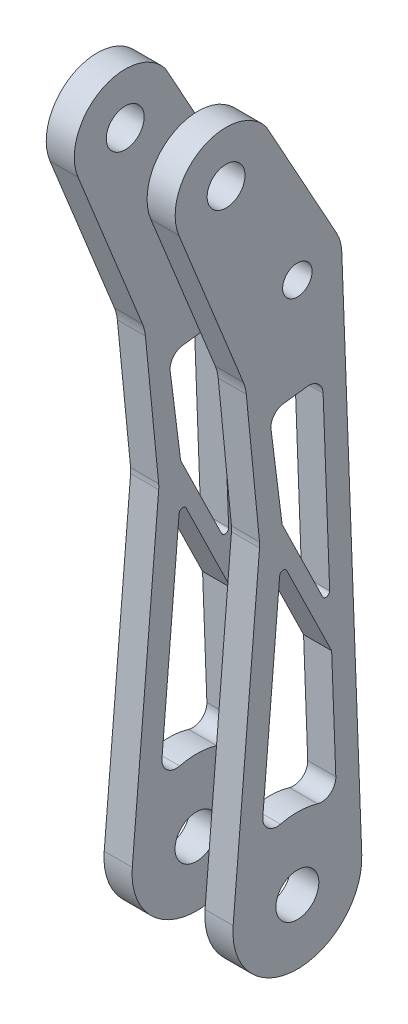
SolidWorks part; units mm, degrees
material "6061-T6 (SS)"
ref_plane "X-Y Datum" through (0, 0, 0) normal (0, 0, 1) x (1, 0, 0)
ref_plane "X-Z Datum" through (0, 0, 0) normal (0, 1, 0) x (1, 0, 0)
ref_plane "Y-Z Datum" through (0, 0, 0) normal (1, 0, 0) x (0, 0, -1)
sketch "Sketch6" plane through (0, 0, 0) normal (1, 0, 0) x (0, 0, -1)
  line L0 (0, 0) -> (0, 95.25) construction
  line L1 (0, 0) -> (0, 118.022) construction
  line L20 (-8.3819, 70.7797) -> (-14.2372, 1.1981)
  line L21 (9.8547, 118.3918) -> (11.5534, 73.1262)
  line L23 (11.5534, 73.1262) -> (14.2775, 0.5358)
  line L24 (-6.91, 150.8965) -> (8.7361, 122.5972)
  line L25 (-26.2646, 139.7057) -> (-11.9697, 104.3659)
  line L26 (-11.3233, 101.7387) -> (-8.39, 71.9341)
  arc A0 (-14.2372, 1.1981) -> (14.2775, 0.5358) centre (0, 0) ccw
  arc A2 (8.7361, 122.5972) -> (9.8547, 118.3918) centre (0, 118.022) cw
  arc A4 (-8.3819, 70.7797) -> (-8.39, 71.9341) centre (-14.7095, 71.3122) ccw
  circle A7 centre (0, 118.022) radius 3.2639
  arc A11 (-26.2646, 139.7057) -> (-6.91, 150.8965) centre (-15.7996, 143.9388) cw
  circle A12 centre (-15.7996, 143.9388) radius 4.1999
  arc A13 (-11.9697, 104.3659) -> (-11.3233, 101.7387) centre (-20.7608, 100.8099) cw
  point P8 (0, 82.55)
  point P12 (0, 82.55)
  point P14 (21.1318, 6.4606)
  point P18 (0, 63.5)
  point P20 (0, 101.6)
  point P23 (0, 0)
  point P24 (0, 0)
  point P25 (11.5534, 73.1262)
  point P26 (-26.2172, 139.5903)
  point P27 (-8.3819, 72.082)
  dimension "D2" = 30.3531
  dimension "D7" = 6.35
  dimension "D8" = 69.5816
  dimension "D5" = 32.3365
  dimension "D3" = 6.5278
  dimension "D4" = 8.3998
  dimension "D10" = 72.5904
  dimension "D11" = 173.041
  dimension "D12" = 206.788
  dimension "D1" = 14.2875
  dimension "D13" = 11.2887
  dimension "D19" = 9.4831
  dimension "D6" = 117.856
  dimension "D9" = 4.81
  dimension "D14" = 25.493
  dimension "D15" = 63.5
  dimension "D16" = 82.55
  dimension "D17" = 101.6
  dimension "D18" = 38.1215
  dimension "D20" = 29.9486
extrude "Boss-Extrude3" add sketch "Sketch6" along normal mid plane 28.575
sketch "Sketch7" plane through (14.2875, 0, 0) normal (1, 0, 0) x (0, 0, -1)
  circle A0 centre (0, 0) radius 4.7625
  dimension "D1" = 9.525
extrude "Cut-Extrude1" cut sketch "Sketch7" against normal blind 7.1437 contours A0
sketch "Sketch8" plane through (7.1437, 0, 0) normal (1, 0, 0) x (0, 0, -1)
  circle A0 centre (0, 0) radius 7.9375
  dimension "D1" = 15.875
extrude "Cut-Extrude2" cut sketch "Sketch8" against normal blind 5.5562 contours A0
mirror "Mirror1" about plane through (0, 0, 0) normal (1, 0, 0) of "Cut-Extrude2"
mirror "Mirror2" about plane through (0, 0, 0) normal (1, 0, 0) of "Cut-Extrude1"
fillet "Fillet1" [suppressed] radius 1.5875
ref_plane "Plane1" through (0, 0, 14.2372) normal (0, 0, -1) x (-1, 0, 0)
sketch "Sketch10" plane through (0, 0, 14.2372) normal (0, 0, -1) x (-1, 0, 0)
  line L0 (-8.0645, 155.9765) -> (-8.0645, -18.6485)
  line L2 (-14.2875, 150.8965) -> (14.2875, 150.8965) construction
  line L4 (8.0645, -18.6485) -> (8.0645, 155.9765)
  line L5 (-8.0645, 155.9765) -> (8.0645, 155.9765)
  line L6 (-4.8895, -21.8235) -> (4.8895, -21.8235)
  arc A1 (4.8895, -21.8235) -> (8.0645, -18.6485) centre (4.8895, -18.6485) ccw
  arc A2 (-4.8895, -21.8235) -> (-8.0645, -18.6485) centre (-4.8895, -18.6485) cw
  point P9 (0, 155.9765)
  dimension "D3" = 177.8
  dimension "D1" = 16.129
  dimension "D2" = 5.08
extrude "Cut-Extrude3" cut sketch "Sketch10" along normal mid plane 58.42
sketch "Sketch11" [suppressed] plane through (-12.7, 0, 0) normal (-1, 0, 0) x (0, 0, 1)
  line L0 (-10.7679, 9.3907) -> (-8.2566, 76.313)
  line L1 (10.3203, 9.8805) -> (4.73, 76.313)
  line L2 (7.8475, 77.1297) -> (14.2372, 1.1981) construction
  line L4 (-14.2775, 0.5358) -> (-9.5183, 127.3572) construction
  arc A0 (10.3203, 9.8805) -> (-10.7679, 9.3907) centre (0, 0) ccw
  arc A1 (-8.2566, 76.313) -> (4.73, 76.313) centre (-1.7633, 89.0398) ccw
  dimension "D1" = 28.575
  dimension "D2" = 28.575
  dimension "D3" = 3.175
  dimension "D4" = 3.175
extrude "Cut-Extrude4" [suppressed] cut sketch "Sketch11" against normal blind 4.7625 contours A1 L1 A0 L0
mirror "Mirror3" [suppressed] about plane through (0, 0, 0) normal (1, 0, 0)
sketch "Sketch12" [suppressed] plane through (0, 0, 0) normal (1, 0, 0) x (0, 0, -1)
  line L0 (0, 95.25) -> (0, 120.65) construction
  line L1 (0, 120.65) -> (24.4512, 127.5273) construction
  line L2 (0, 95.25) -> (-24.8767, 90.1209) construction
  line L3 (0, 127) -> (326.3698, 134.0383) construction
  line L4 (0, 95.25) -> (0, 69.85) construction
  dimension "D1" = 50.8
  dimension "D2" = 78.35
  dimension "D3" = 25.4
  dimension "D4" = 25.4
sketch "Sketch13" plane through (14.2875, 0, 0) normal (1, 0, 0) x (0, 0, -1)
  line L0 (-3.3694, 72.7427) -> (-6.2305, 95.423)
  line L2 (-6.2305, 95.423) -> (5.5772, 96.9125)
  line L9 (-3.3198, 70.3537) -> (-8.0907, 13.6586)
  line L10 (5.5772, 96.9125) -> (8.7161, 13.2682)
  line L12 (-8.3819, 70.7797) -> (-14.2372, 1.1981) construction
  line L13 (14.2775, 0.5358) -> (9.8547, 118.3918) construction
  arc A1 (8.7161, 13.2682) -> (-8.0907, 13.6586) centre (0, 0) ccw
  arc A2 (-3.3694, 72.7427) -> (-3.3198, 70.3537) centre (-14.7095, 71.3122) cw
  dimension "D3" = 15.875
  dimension "D4" = 11.43
  dimension "D2" = 22.86
  dimension "D5" = 12
  dimension "D6" = 5.08
  dimension "D7" = 5.08
  dimension "D1" = 11.9013
extrude "Cut-Extrude5" cut sketch "Sketch13" against normal blind 28.575 contours L2 L10 A1 L9 A2 L0
fillet "Fillet2" radius 3.175 4 edges at (-11.176, 95.423, 6.2305) (-11.176, 96.9125, -5.5772) (-11.176, 13.2682, -8.7161) (-11.176, 13.6586, 8.0907)
fillet "Fillet3" radius 3.175 4 edges at (11.176, 95.423, 6.2305) (11.176, 13.2682, -8.7161) (11.176, 13.6586, 8.0907) (11.176, 96.9125, -5.5772)
sketch "Sketch21" plane through (14.2875, 0, 0) normal (1, 0, 0) x (0, 0, -1)
  line L0 (-3.3694, 72.7427) -> (7.3045, 50.8849)
  line L1 (5.7072, 93.4476) -> (8.5234, 18.4022) construction
  line L2 (-3.6749, 66.1329) -> (7.5986, 43.047)
  line L3 (-3.3198, 70.3537) -> (-7.6599, 18.7781) construction
  line L4 (7.5986, 43.047) -> (7.3045, 50.8849)
  line L5 (-3.6749, 66.1329) -> (-3.3198, 70.3537)
  arc A0 (-3.3198, 70.3537) -> (-3.3694, 72.7427) centre (-14.7095, 71.3122) ccw
  dimension "D1" = 3.175
  dimension "D2" = 210.838
extrude "Boss-Extrude4" add sketch "Sketch21" against normal up to surface (6.223 mm away) up to face at (8.0645, 58.8813, 0.6223)
fillet "Fillet4" radius 0.8255 2 edges at (11.176, 66.1329, 3.6749) (11.176, 50.8849, -7.3045)
sketch "Sketch23" plane through (-14.2875, 0, -12.7) normal (1, 0, 0) x (0, 0, -1)
  line L0 (-16.3614, 74.2421) -> (-5.4322, 51.8613)
  line L2 (-16.3102, 66.9017) -> (-5.1381, 44.0234)
  line L4 (-5.1381, 44.0234) -> (-5.4322, 51.8613)
  line L5 (-16.3102, 66.9017) -> (-16.0198, 70.3537)
  line L6 (-6.9928, 93.4476) -> (-4.1766, 18.4022) construction
  arc A0 (-16.0198, 70.3537) -> (-16.3614, 74.2421) centre (-27.4095, 71.3122) ccw
  arc A1 (-16.0198, 70.3537) -> (-16.0694, 72.7427) centre (-27.4095, 71.3122) ccw construction
  dimension "D1" = 3.175
  dimension "D2" = 210.838
extrude "Boss-Extrude5" add sketch "Sketch23" along normal up to surface (6.223 mm away) up to face at (-8.0645, 58.8813, 0.6223)
fillet "Fillet6" radius 0.8255 2 edges at (-11.176, 51.8613, -7.2678) (-11.176, 66.9017, 3.6102)
ref_plane "Plane2" through (26.9875, 0, 0) normal (1, 0, 0) x (0, 0, -1)
sketch "Sketch17" plane through (-14.2875, 0, 0) normal (-1, 0, 0) x (0, 0, 1)
  line L1 (-15.7464, -15.0456) -> (16.41, -15.0456)
  line L2 (-15.7464, -15.0456) -> (-15.7464, 137.8624)
  line L3 (-15.7464, 137.8624) -> (16.41, 137.8624)
  line L4 (16.41, -15.0456) -> (16.41, 137.8624)
  arc A0 (-14.2775, 0.5358) -> (14.2372, 1.1981) centre (0, 0) ccw construction
  point P8 (0.3318, -14.2836)
  point P9 (0.3318, -15.0456)
  dimension "D1" = 152.908
  dimension "D2" = 32.1564
  dimension "D3" = 0.762
sketch "Sketch18" plane through (26.9875, 0, 0) normal (1, 0, 0) x (0, 0, -1)
  point P0 (0, 0)
sketch3d "3DSketch1"
  line L0 (14.2875, 0, 0) -> (-14.2875, 0, 0) construction
  line L1 (8.0645, 0, 0) -> (14.2875, 0, 0) construction
  line L2 (14.2875, 0, 0) -> (8.0645, 0, 0) construction
  line L4 (-8.0645, 0, 0) -> (-14.2875, 0, 0) construction
  point P10 (0, 0, 0)
sketch3d "3DSketch2"
  line L0 (14.2875, 143.9388, 15.7996) -> (-14.2875, 143.9388, 15.7996) construction
  line L3 (14.2875, 118.022, 0) -> (-14.2875, 118.022, 0) construction
  line L4 (14.2875, 118.022, 0) -> (8.0645, 118.022, 0) construction
  line L5 (-8.0645, 118.022, 0) -> (-14.2875, 118.022, 0) construction
  circle A0 centre (-14.2875, 143.9388, 15.7996) radius 4.1999 construction
  point P5 (-10.0876, 143.9388, 15.7996)
  point P6 (0, 143.9388, 15.7996)
  point P13 (0, 118.022, 0)
sketch "Sketch19" plane through (0, 0, 0) normal (0, 0, 1) x (1, 0, 0)
  line L0 (0, 0) -> (0, -38.1) construction
  dimension "D1" = 38.1
